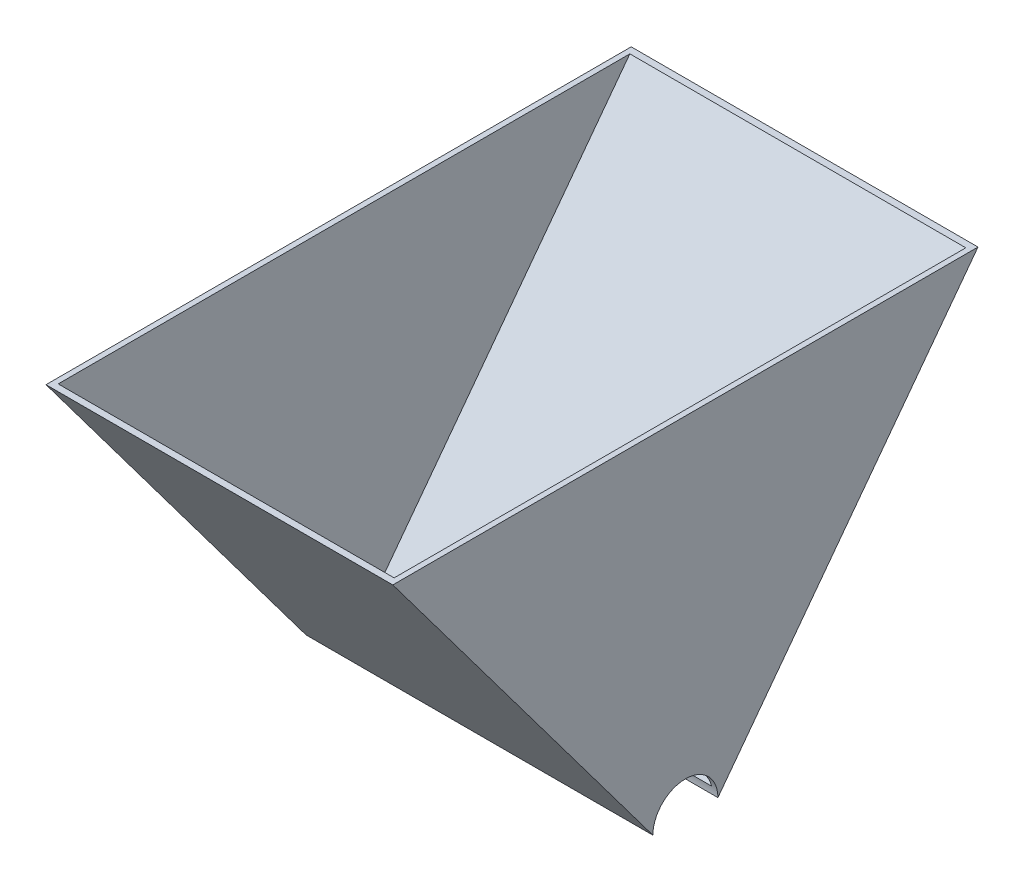
SolidWorks part; units mm, degrees
ref_plane "Front Plane" through (0, 0, 0) normal (0, 0, 1) x (1, 0, 0)
ref_plane "Top Plane" through (0, 0, 0) normal (0, 1, 0) x (1, 0, 0)
ref_plane "Right Plane" through (0, 0, 0) normal (1, 0, 0) x (0, 0, -1)
sketch "Sketch1" plane through (0, 0, 0) normal (1, 0, 0) x (0, 0, -1)
  line L0 (-9.525, 0) -> (-85.725, 101.6)
  line L1 (-85.725, 101.6) -> (85.725, 101.6)
  line L2 (85.725, 101.6) -> (9.525, 0)
  arc A0 (-9.525, 0) -> (9.525, 0) centre (0, 0) cw
  dimension "D1" = 9.525
  dimension "D2" = 171.45
  dimension "D3" = 127
  dimension "D4" = 127
extrude "Boss-Extrude1" add sketch "Sketch1" along normal blind 101.6
shell "Shell3" thickness 1.5875
